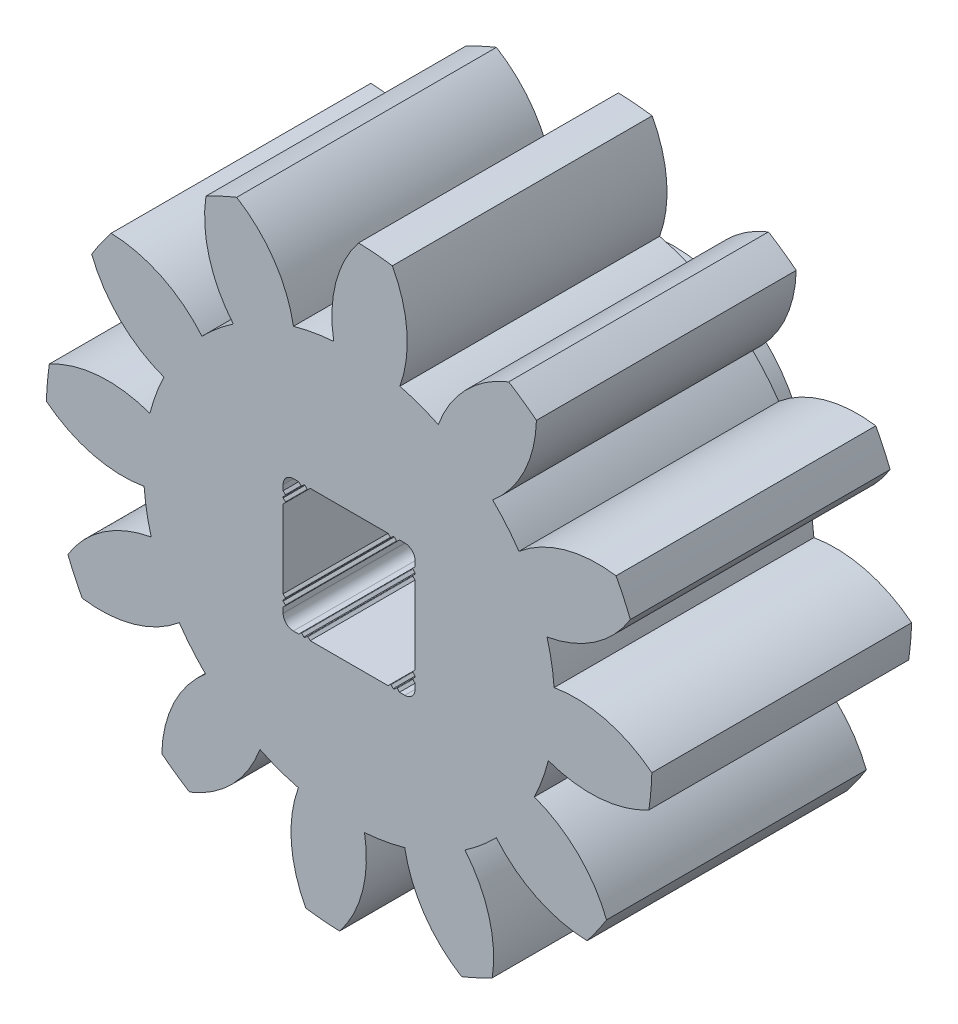
SolidWorks part; units mm, degrees
ref_plane "Front Plane" through (0, 0, 0) normal (0, 0, 1) x (1, 0, 0)
ref_plane "Top Plane" through (0, 0, 0) normal (0, 1, 0) x (1, 0, 0)
ref_plane "Right Plane" through (0, 0, 0) normal (1, 0, 0) x (0, 0, -1)
sketch "Sketch1" plane through (0, 0, 0) normal (0, 1, 0) x (1, 0, 0)
  line L0 (7.404, 3.175) -> (0, 3.175)
  line L1 (0, 3.175) -> (0, -3.175)
  line L2 (0, -3.175) -> (7.404, -3.175)
  line L3 (7.404, -3.175) -> (7.404, 3.175)
  line L4 (0, 3.175) -> (0, -3.175) construction
revolve "Revolve1" add sketch "Sketch1" angle 360 about L4
sketch "Sketch2" plane through (0, 0, -3.175) normal (0, 0, -1) x (-1, 0, 0)
  arc A0 (1.057, -7.3282) -> (3.9007, -6.2931) centre (0, 0) ccw
  arc A1 (3.9007, -6.2931) -> (2.1801, -4.528) centre (4.999, -3.5014) cw
  arc A2 (2.1801, -4.528) -> (1.2404, -4.87) centre (0, 0) cw
  arc A3 (1.2404, -4.87) -> (1.057, -7.3282) centre (-1.5788, -5.8955) cw
extrude "Cut-Extrude1" cut sketch "Sketch2" against normal through all
sketch "Sketch3" plane through (0, 0, -3.175) normal (0, 0, -1) x (-1, 0, 0)
  arc A0 (-2.7487, -6.8749) -> (0.2316, -7.4004) centre (0, 0) ccw
  arc A1 (0.2316, -7.4004) -> (-0.3759, -5.0114) centre (2.5786, -5.5318) cw
  arc A2 (-0.3759, -5.0114) -> (-1.3607, -4.8378) centre (0, 0) cw
  arc A3 (-1.3607, -4.8378) -> (-2.7487, -6.8749) centre (-4.3151, -4.3163) cw
extrude "Cut-Extrude2" cut sketch "Sketch3" against normal through all
sketch "Sketch4" plane through (0, 0, -3.175) normal (0, 0, -1) x (-1, 0, 0)
  arc A0 (-5.8179, -4.5795) -> (-3.4996, -6.5247) centre (0, 0) ccw
  arc A1 (-3.4996, -6.5247) -> (-2.8313, -4.152) centre (-0.5328, -6.08) cw
  arc A2 (-2.8313, -4.152) -> (-3.5973, -3.5093) centre (0, 0) cw
  arc A3 (-3.5973, -3.5093) -> (-5.8179, -4.5795) centre (-5.8951, -1.5805) cw
extrude "Cut-Extrude3" cut sketch "Sketch4" against normal through all
sketch "Sketch5" plane through (0, 0, -3.175) normal (0, 0, -1) x (-1, 0, 0)
  arc A0 (-7.3282, -1.057) -> (-6.2931, -3.9007) centre (0, 0) ccw
  arc A1 (-6.2931, -3.9007) -> (-4.528, -2.1801) centre (-3.5014, -4.999) cw
  arc A2 (-4.528, -2.1801) -> (-4.87, -1.2404) centre (0, 0) cw
  arc A3 (-4.87, -1.2404) -> (-7.3282, -1.057) centre (-5.8955, 1.5788) cw
extrude "Cut-Extrude4" cut sketch "Sketch5" against normal through all
sketch "Sketch6" plane through (0, 0, -3.175) normal (0, 0, -1) x (-1, 0, 0)
  arc A0 (-6.8749, 2.7487) -> (-7.4004, -0.2316) centre (0, 0) ccw
  arc A1 (-7.4004, -0.2316) -> (-5.0114, 0.3759) centre (-5.5318, -2.5786) cw
  arc A2 (-5.0114, 0.3759) -> (-4.8378, 1.3607) centre (0, 0) cw
  arc A3 (-4.8378, 1.3607) -> (-6.8749, 2.7487) centre (-4.3163, 4.3151) cw
extrude "Cut-Extrude5" cut sketch "Sketch6" against normal through all
sketch "Sketch7" plane through (0, 0, -3.175) normal (0, 0, -1) x (-1, 0, 0)
  arc A0 (-4.5795, 5.8179) -> (-6.5247, 3.4996) centre (0, 0) ccw
  arc A1 (-6.5247, 3.4996) -> (-4.152, 2.8313) centre (-6.08, 0.5328) cw
  arc A2 (-4.152, 2.8313) -> (-3.5093, 3.5973) centre (0, 0) cw
  arc A3 (-3.5093, 3.5973) -> (-4.5795, 5.8179) centre (-1.5805, 5.8951) cw
extrude "Cut-Extrude6" cut sketch "Sketch7" against normal through all
sketch "Sketch8" plane through (0, 0, -3.175) normal (0, 0, -1) x (-1, 0, 0)
  arc A0 (-1.057, 7.3282) -> (-3.9007, 6.2931) centre (0, 0) ccw
  arc A1 (-3.9007, 6.2931) -> (-2.1801, 4.528) centre (-4.999, 3.5014) cw
  arc A2 (-2.1801, 4.528) -> (-1.2404, 4.87) centre (0, 0) cw
  arc A3 (-1.2404, 4.87) -> (-1.057, 7.3282) centre (1.5788, 5.8955) cw
extrude "Cut-Extrude7" cut sketch "Sketch8" against normal through all
sketch "Sketch9" plane through (0, 0, -3.175) normal (0, 0, -1) x (-1, 0, 0)
  arc A0 (2.7487, 6.8749) -> (-0.2316, 7.4004) centre (0, 0) ccw
  arc A1 (-0.2316, 7.4004) -> (0.3759, 5.0114) centre (-2.5786, 5.5318) cw
  arc A2 (0.3759, 5.0114) -> (1.3607, 4.8378) centre (0, 0) cw
  arc A3 (1.3607, 4.8378) -> (2.7487, 6.8749) centre (4.3151, 4.3163) cw
extrude "Cut-Extrude8" cut sketch "Sketch9" against normal through all
sketch "Sketch10" plane through (0, 0, -3.175) normal (0, 0, -1) x (-1, 0, 0)
  arc A0 (5.8179, 4.5795) -> (3.4996, 6.5247) centre (0, 0) ccw
  arc A1 (3.4996, 6.5247) -> (2.8313, 4.152) centre (0.5328, 6.08) cw
  arc A2 (2.8313, 4.152) -> (3.5973, 3.5093) centre (0, 0) cw
  arc A3 (3.5973, 3.5093) -> (5.8179, 4.5795) centre (5.8951, 1.5805) cw
extrude "Cut-Extrude9" cut sketch "Sketch10" against normal through all
sketch "Sketch11" plane through (0, 0, -3.175) normal (0, 0, -1) x (-1, 0, 0)
  arc A0 (7.3282, 1.057) -> (6.2931, 3.9007) centre (0, 0) ccw
  arc A1 (6.2931, 3.9007) -> (4.528, 2.1801) centre (3.5014, 4.999) cw
  arc A2 (4.528, 2.1801) -> (4.87, 1.2404) centre (0, 0) cw
  arc A3 (4.87, 1.2404) -> (7.3282, 1.057) centre (5.8955, -1.5788) cw
extrude "Cut-Extrude10" cut sketch "Sketch11" against normal through all
sketch "Sketch12" plane through (0, 0, -3.175) normal (0, 0, -1) x (-1, 0, 0)
  arc A0 (6.8749, -2.7487) -> (7.4004, 0.2316) centre (0, 0) ccw
  arc A1 (7.4004, 0.2316) -> (5.0114, -0.3759) centre (5.5318, 2.5786) cw
  arc A2 (5.0114, -0.3759) -> (4.8378, -1.3607) centre (0, 0) cw
  arc A3 (4.8378, -1.3607) -> (6.8749, -2.7487) centre (4.3163, -4.3151) cw
extrude "Cut-Extrude11" cut sketch "Sketch12" against normal through all
sketch "Sketch13" plane through (0, 0, -3.175) normal (0, 0, -1) x (-1, 0, 0)
  arc A0 (4.5795, -5.8179) -> (6.5247, -3.4996) centre (0, 0) ccw
  arc A1 (6.5247, -3.4996) -> (4.152, -2.8313) centre (6.08, -0.5328) cw
  arc A2 (4.152, -2.8313) -> (3.5093, -3.5973) centre (0, 0) cw
  arc A3 (3.5093, -3.5973) -> (4.5795, -5.8179) centre (1.5805, -5.8951) cw
extrude "Cut-Extrude12" cut sketch "Sketch13" against normal through all
sketch "Sketch14" plane through (0, 0, 3.175) normal (0, 0, 1) x (1, 0, 0)
  circle A0 centre (0, 0) radius 3.25
sketch "Sketch15" plane through (0, 0, -3.175) normal (0, 0, -1) x (-1, 0, 0)
  circle A0 centre (0, 0) radius 3.25
extrude "Boss-Extrude2" add sketch "Sketch15" along normal blind 1.5875
sketch "Sketch16" plane through (0, 0, -4.7625) normal (0, 0, -1) x (-1, 0, 0)
  line L0 (1.5488, 1.1682) -> (1.6125, 1.2315)
  line L1 (1.6125, 1.2315) -> (1.6125, 1.6125)
  line L2 (1.6125, 1.6125) -> (1.2315, 1.6125)
  line L3 (1.2315, 1.6125) -> (1.168, 1.549)
  line L4 (1.168, 1.549) -> (1.0918, 1.6252)
  line L5 (1.0918, 1.6252) -> (1.0156, 1.549)
  line L6 (1.0156, 1.549) -> (0.9521, 1.6125)
  line L7 (0.9521, 1.6125) -> (-0.9521, 1.6125)
  line L8 (-0.9521, 1.6125) -> (-1.0156, 1.5488)
  line L9 (-1.0156, 1.5488) -> (-1.0918, 1.6252)
  line L10 (-1.0918, 1.6252) -> (-1.168, 1.5488)
  line L11 (-1.168, 1.5488) -> (-1.2315, 1.6125)
  line L12 (-1.2315, 1.6125) -> (-1.6125, 1.6125)
  line L13 (-1.6125, 1.6125) -> (-1.6125, 1.2315)
  line L14 (-1.6125, 1.2315) -> (-1.5488, 1.168)
  line L15 (-1.5488, 1.168) -> (-1.6252, 1.0918)
  line L16 (-1.6252, 1.0918) -> (-1.5488, 1.0156)
  line L17 (-1.5488, 1.0156) -> (-1.6125, 0.9521)
  line L18 (-1.6125, 0.9521) -> (-1.6125, -0.9521)
  line L19 (-1.6125, -0.9521) -> (-1.549, -1.0156)
  line L20 (-1.549, -1.0156) -> (-1.6252, -1.0918)
  line L21 (-1.6252, -1.0918) -> (-1.5488, -1.1682)
  line L22 (-1.5488, -1.1682) -> (-1.6125, -1.2315)
  line L23 (-1.6125, -1.2315) -> (-1.6125, -1.6125)
  line L24 (-1.6125, -1.6125) -> (-1.2315, -1.6125)
  line L25 (-1.2315, -1.6125) -> (-1.168, -1.549)
  line L26 (-1.168, -1.549) -> (-1.0918, -1.6252)
  line L27 (-1.0918, -1.6252) -> (-1.0156, -1.549)
  line L28 (-1.0156, -1.549) -> (-0.9521, -1.6125)
  line L29 (-0.9521, -1.6125) -> (0.9521, -1.6125)
  line L30 (0.9521, -1.6125) -> (1.0156, -1.5488)
  line L31 (1.0156, -1.5488) -> (1.0918, -1.6252)
  line L32 (1.0918, -1.6252) -> (1.168, -1.5488)
  line L33 (1.168, -1.5488) -> (1.2315, -1.6125)
  line L34 (1.2315, -1.6125) -> (1.6125, -1.6125)
  line L35 (1.6125, -1.6125) -> (1.6125, -1.2315)
  line L36 (1.6125, -1.2315) -> (1.5488, -1.168)
  line L37 (1.5488, -1.168) -> (1.6252, -1.0918)
  line L38 (1.6252, -1.0918) -> (1.5488, -1.0156)
  line L39 (1.5488, -1.0156) -> (1.6125, -0.9521)
  line L40 (1.6125, -0.9521) -> (1.6125, 0.9521)
  line L41 (1.6125, 0.9521) -> (1.549, 1.0156)
  line L42 (1.549, 1.0156) -> (1.6252, 1.0918)
  line L43 (1.6252, 1.0918) -> (1.5488, 1.1682)
extrude "Cut-Extrude13" cut sketch "Sketch16" against normal through all
fillet "Fillet1" radius 0.0127 16 edges at (1.168, -1.549, -0.7938) (-1.168, 1.549, -0.7938) (1.5488, 1.0156, -0.7938) (1.5488, 1.168, -0.7938) (-1.0156, 1.549, -0.7938) (1.168, 1.5488, -0.7938) (1.5488, -1.1682, -0.7938) (-1.168, -1.5488, -0.7938) (1.0156, 1.5488, -0.7938) (-1.0156, -1.5488, -0.7938) (1.549, -1.0156, -0.7938) (1.0156, -1.549, -0.7938) (-1.5488, -1.0156, -0.7938) (-1.549, 1.0156, -0.7938) (-1.5488, 1.1682, -0.7938) (-1.5488, -1.168, -0.7938)
chamfer "Chamfer1" distance 0.018 angle 45 4 edges at (1.0918, -1.6252, -0.7938) (-1.0918, 1.6252, -0.7938) (1.6252, -1.0918, -0.7938) (-1.6252, 1.0918, -0.7938)
chamfer "Chamfer2" distance 0.018 angle 45.095 4 edges at (1.6252, 1.0918, -0.7938) (-1.0918, -1.6252, -0.7938) (-1.6252, -1.0918, -0.7938) (1.0918, 1.6252, -0.7938)
fillet "Fillet2" radius 0.25 4 edges at (-1.6125, -1.6125, -0.7938) (1.6125, 1.6125, -0.7938) (-1.6125, 1.6125, -0.7938) (1.6125, -1.6125, -0.7938)
